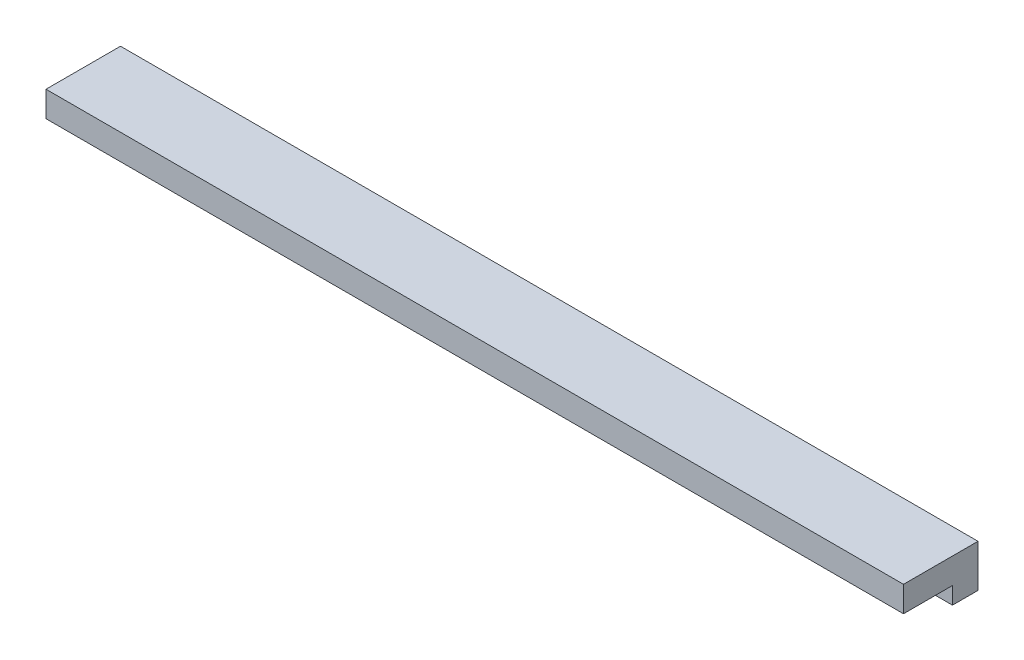
SolidWorks part; units mm, degrees
ref_plane "前视基准面" through (0, 0, 0) normal (0, 0, 1) x (1, 0, 0)
ref_plane "上视基准面" through (0, 0, 0) normal (0, 1, 0) x (1, 0, 0)
ref_plane "右视基准面" through (0, 0, 0) normal (1, 0, 0) x (0, 0, -1)
sketch "草图2" plane through (-123.0497, 0, 0) normal (-1, 0, 0) x (0, 0, 1)
  line L0 (0, -3.7034) -> (0, -8.7034)
  line L1 (0, -98.2034) -> (0, 41.7966) construction
  line L2 (8.75, -6.7034) -> (3, -6.7034)
  line L3 (8.75, -6.7034) -> (8.75, -3.7034)
  line L4 (8.75, -3.7034) -> (0, -3.7034)
  line L5 (3, -6.7034) -> (3, -8.7034)
  line L6 (0, -8.7034) -> (8.9877, -8.7034) construction
  line L7 (3, -8.7034) -> (0, -8.7034)
  line L9 (0, -8.7034) -> (8.9877, -8.7034) construction
  line L10 (8.75, -18.7034) -> (8.75, -8.7034) construction
  line L11 (8.75, -18.7034) -> (8.75, -8.7034) construction
  dimension "D1" = 2
  dimension "D2" = 3
  dimension "D3" = 3
extrude "凸台-拉伸1" add sketch "草图2" against normal offset from surface (100.7005 mm away) 10
